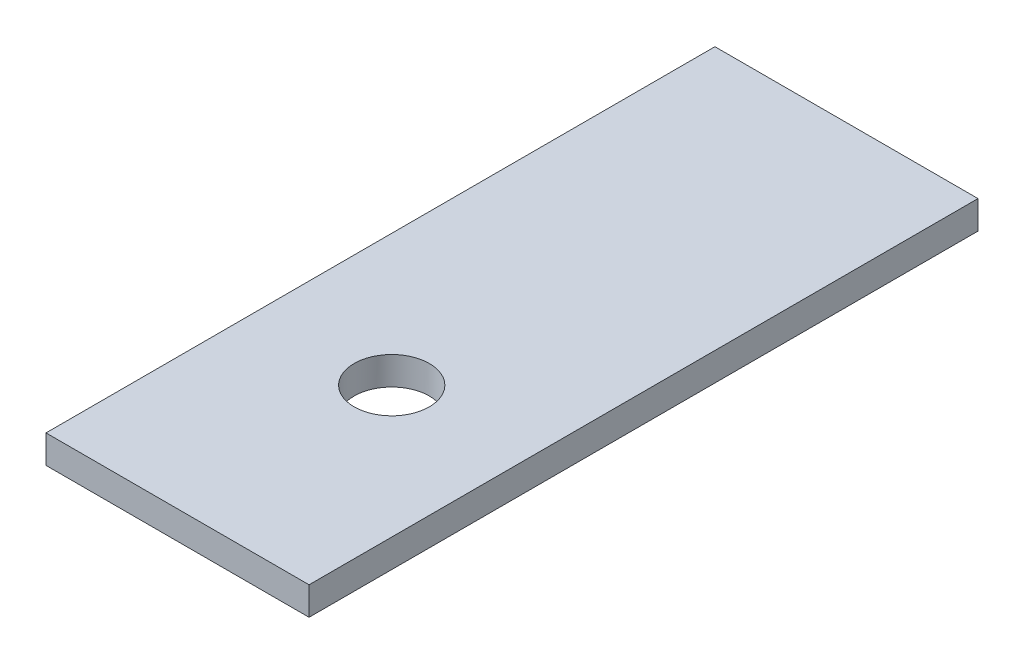
SolidWorks part; units mm, degrees
material "Custom Plastic"
ref_plane "Front Plane" through (0, 0, 0) normal (0, 0, 1) x (1, 0, 0)
ref_plane "Top Plane" through (0, 0, 0) normal (0, 1, 0) x (1, 0, 0)
ref_plane "Right Plane" through (0, 0, 0) normal (1, 0, 0) x (0, 0, -1)
sketch "Sketch1" plane through (0, 0, 0) normal (0, 1, 0) x (1, 0, 0)
  line L1 (-14, -35.6) -> (14, -35.6)
  line L2 (-14, -35.6) -> (-14, 35.6)
  line L3 (-14, 35.6) -> (14, 35.6)
  line L4 (14, -35.6) -> (14, 35.6)
  line L5 (-14, -35.6) -> (14, 35.6) construction
  line L6 (-14, 35.6) -> (14, -35.6) construction
  point P0 (0, 0)
  dimension "D1" = 71.2
  dimension "D2" = 28
extrude "Boss-Extrude1" add sketch "Sketch1" along normal blind 3
sketch "Sketch4" plane through (0, 3, 0) normal (0, 1, 0) x (1, 0, 0)
  line L0 (0, -2.5883) -> (0, -23.7562) construction
  line L1 (14, -35.6) -> (14, 35.6) construction
  circle A0 centre (7, -12.8) radius 1
  circle A1 centre (0, -19.8) radius 1
  circle A2 centre (-7, -12.8) radius 1
  circle A4 centre (0, -5.8) radius 1
  circle A9 centre (0, -12.8) radius 7 construction
  point P18 (0, -12.8)
  dimension "D1" = 2
  dimension "D2" = 14
  dimension "D4" = 14
  dimension "D3" = 4
extrude "Cut-Extrude2" cut sketch "Sketch4" against normal blind 10
sketch "Sketch5" plane through (0, 3, 0) normal (0, 1, 0) x (1, 0, 0)
  line L2 (-14, -35.6) -> (14, -35.6) construction
  line L3 (14, -35.6) -> (14, 35.6) construction
  circle A0 centre (0, -12.8) radius 4
  dimension "D1" = 8
  dimension "D2" = 22.8
  dimension "D3" = 14
extrude "Cut-Extrude3" cut sketch "Sketch5" against normal blind 10
sketch "Sketch9" plane through (0, 3, 0) normal (0, 1, 0) x (1, 0, 0)
  circle A1 centre (-9.2488, -28.4482) radius 1.75
  circle A2 centre (-9.2488, -28.4482) radius 1.75
  circle A3 centre (10.0812, 20.9482) radius 1.75
  circle A4 centre (10.0812, 20.9482) radius 1.75
  circle A5 centre (9.8488, 28.4482) radius 1.75
  circle A6 centre (9.8488, 28.4482) radius 1.75
  circle A7 centre (-3.9188, 20.9482) radius 1.75
  circle A8 centre (-3.9188, 20.9482) radius 1.75
  circle A9 centre (-3.9188, 28.4482) radius 1.75
  circle A10 centre (-3.9188, 28.4482) radius 1.75
  circle A11 centre (4.5188, -20.9482) radius 1.75
  circle A12 centre (4.5188, -20.9482) radius 1.75
  circle A13 centre (4.5188, -28.4482) radius 1.75
  circle A14 centre (4.5188, -28.4482) radius 1.75
  circle A15 centre (-9.4812, -20.9482) radius 1.75
  circle A16 centre (-9.4812, -20.9482) radius 1.75
  dimension "D1" = 0
  dimension "D2" = 0
  dimension "D3" = 0
  dimension "D4" = 0
  dimension "D5" = 0
  dimension "D6" = 0
  dimension "D7" = 0
  dimension "D8" = 0
sketch "Sketch10" plane through (0, 3, 0) normal (0, 1, 0) x (1, 0, 0)
  circle A0 centre (0, -19.8) radius 1.75
  circle A1 centre (-7, -12.8) radius 1.75
  circle A2 centre (0, -5.8) radius 1.75
  circle A3 centre (7, -12.8) radius 1.75
  dimension "D1" = 3.5
  dimension "D2" = 3.5
  dimension "D3" = 3.5
  dimension "D4" = 3.5
extrude "Cut-Extrude9" cut sketch "Sketch10" against normal blind 1.6
sketch "Sketch12" plane through (0, 3, 0) normal (0, 1, 0) x (1, 0, 0)
  circle A0 centre (0, -19.8) radius 1.75 construction
  circle A1 centre (-7, -12.8) radius 1.75 construction
  circle A2 centre (0, -5.8) radius 1.75 construction
  circle A3 centre (7, -12.8) radius 1.75 construction
  circle A4 centre (0, -19.8) radius 1.75
  circle A5 centre (-7, -12.8) radius 1.75
  circle A6 centre (0, -5.8) radius 1.75
  circle A7 centre (7, -12.8) radius 1.75
extrude "Boss-Extrude2" add sketch "Sketch12" against normal up to surface (3 mm away) up to face at (0, 0, 8.8)
